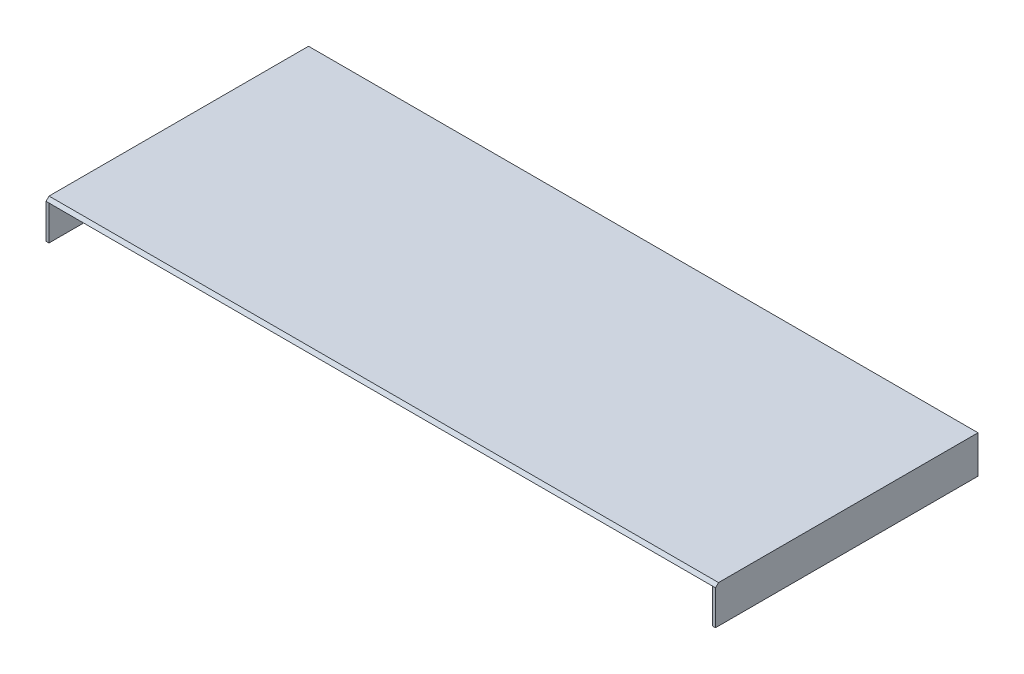
SolidWorks part; units mm, degrees
material "PPS"
ref_plane "Płaszczyzna XY" through (0, 0, 0) normal (0, 0, 1) x (1, 0, 0)
ref_plane "Płaszczyzna XZ" through (0, 0, 0) normal (0, 1, 0) x (1, 0, 0)
ref_plane "Płaszczyzna YZ" through (0, 0, 0) normal (1, 0, 0) x (0, 0, -1)
sketch "Szkic3" plane through (0, 0, 0) normal (1, 0, 0) x (0, 0, -1)
  line L0 (0, 0) -> (-150, 0)
  line L4 (-151.75, -1.75) -> (0, -1.75)
  line L5 (0, -1.75) -> (0, 0)
  line L6 (-151.75, -1.75) -> (-150, 0)
  dimension "D1" = 150
  dimension "D2" = 135
  dimension "D4" = 1.75
  dimension "D5" = 0
  dimension "D6" = 0
extrude "Dodanie-wyciągnięcie3" add sketch "Szkic3" along normal mid plane 387
sketch "Szkic4" plane through (0, -1.75, 0) normal (0, -1, 0) x (1, 0, 0)
  line L0 (-193.5, 151.75) -> (-193.5, 0)
  line L1 (193.5, 151.75) -> (-193.5, 151.75) construction
  line L2 (193.5, 0) -> (-193.5, 0) construction
  line L3 (-193.5, 151.75) -> (-193.5, 0) construction
  line L4 (-193.5, 0) -> (193.5, 0)
  line L5 (193.5, 151.75) -> (193.5, 0) construction
  line L6 (193.5, 0) -> (193.5, 151.75)
  line L7 (193.5, 151.75) -> (191.75, 151.75)
  line L8 (191.75, 151.75) -> (191.75, 1.75)
  line L9 (191.75, 1.75) -> (-191.75, 1.75)
  line L10 (-191.75, 1.75) -> (-191.75, 151.75)
  line L11 (-191.75, 151.75) -> (-193.5, 151.75)
  dimension "D1" = 1.75
  dimension "D2" = 1.75
  dimension "D3" = 1.75
extrude "Dodanie-wyciągnięcie4" add sketch "Szkic4" along normal blind 20
